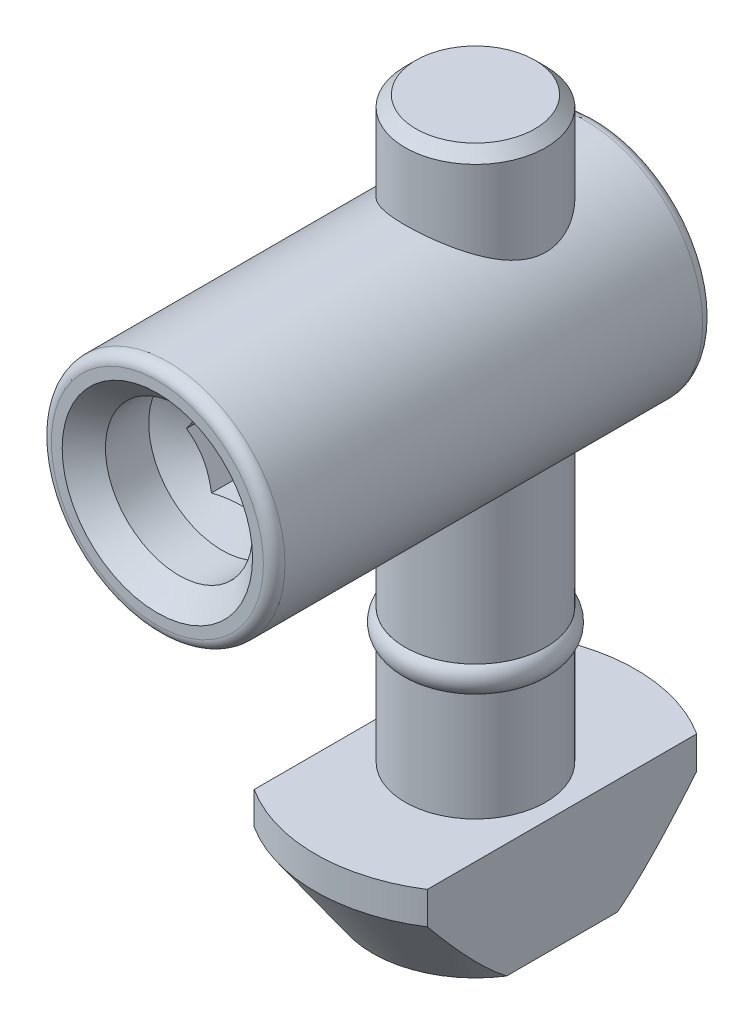
SolidWorks part; units mm, degrees
ref_plane "Спереди" through (0, 0, 0) normal (0, 0, 1) x (1, 0, 0)
ref_plane "Сверху" through (0, 0, 0) normal (0, 1, 0) x (1, 0, 0)
ref_plane "Справа" through (0, 0, 0) normal (1, 0, 0) x (0, 0, -1)
sketch "Эскиз3" plane through (0, 0, 0) normal (0, 0, 1) x (1, 0, 0)
  line L0 (0, 0) -> (-3.25, 0)
  line L1 (-3.25, 0) -> (-3.25, -20.5)
  line L2 (-3.25, -20.5) -> (-2.75, -20.5)
  line L3 (-2.75, -20.5) -> (-2.75, -21.7)
  line L4 (-2.75, -21.7) -> (-3.25, -21.7)
  line L5 (-3.25, -21.7) -> (-3.25, -26.7)
  line L7 (0, -32) -> (0, 0)
  line L8 (0, 0) -> (0, 5.384) construction
  line L9 (-3.25, -26.7) -> (-7.4, -26.7)
  line L10 (-7.4, -26.7) -> (-7.4, -28.2)
  line L11 (-7.4, -28.2) -> (-4.75, -32)
  line L12 (-4.75, -32) -> (0, -32)
  point P3 (0, -29.8286)
  point P9 (-4.2202, -32)
  dimension "D1" = 6.5
  dimension "D2" = 1.2
  dimension "D3" = 32
  dimension "D4" = 0.5
  dimension "D5" = 5
  dimension "D6" = 5.3
  dimension "D7" = 1.5
  dimension "D8" = 1.5
  dimension "D9" = 14.8
revolve "Повернуть1" add sketch "Эскиз3" angle 360 about L8
sketch "Эскиз6" plane through (0, -32, 0) normal (0, -1, 0) x (1, 0, 0)
  line L1 (-4, -7.4) -> (4, -7.4)
  line L2 (-4, -7.4) -> (-4, 7.4)
  line L3 (-4, 7.4) -> (4, 7.4)
  line L4 (4, -7.4) -> (4, 7.4)
  line L5 (-4, -7.4) -> (4, 7.4) construction
  line L6 (-4, 7.4) -> (4, -7.4) construction
  circle A1 centre (0, 0) radius 7.4 construction
  point P0 (0, 0)
  dimension "D1" = 8
extrude "Вырез-Вытянуть1" cut sketch "Эскиз6" against normal up to surface (5.3 mm away) flip side to cut up to face at (0, -26.7, -7.4)
chamfer "Фаска1" distance 0.5 angle 45 1 edges at (0, 0, -3.25)
sketch "Эскиз12" plane through (0, 0, 0) normal (0, 0, 1) x (1, 0, 0)
  line L0 (2.75, 0) -> (-2.75, 0) construction
  circle A0 centre (0, -9) radius 5.4
  point P4 (1.0261, -9)
  dimension "D1" = 10.8
  dimension "D2" = 9
extrude "Бобышка-Вытянуть2" add sketch "Эскиз12" along normal blind 14.7 and the other way blind 5.6
hole_wizard "Отверстие обработанное метчиком M81" positions "Эскиз13" profile "Эскиз14" tap size "M8" standard "ISO"
sketch "Эскиз13" plane through (0, 0, 14.7) normal (0, 0, 1) x (1, 0, 0)
  point P0 (0, -9)
cosmetic thread "Отверстие резьбы1" parameters "D1"=3, "D2"=8
sketch "Эскиз14" plane through (0, -9, 14.7) normal (1, 0, 0) x (0, -1, 0)
  line L0 (0, 0) -> (0, 5.0429)
  line L1 (0, 5.0429) -> (3.4, 3)
  line L2 (3.4, 3) -> (3.4, 1)
  line L3 (3.4, 1) -> (4.4, 0)
  line L5 (4.4, 0) -> (0, 0)
  line L6 (-3.4, 1) -> (-4.4, 0) construction
  line L10 (0, 5.0429) -> (-3.4, 3) construction
  line L11 (0, -6.35) -> (0, 107.95) construction
  dimension "Диаметр сверла" = 6.8
  dimension "Глубина сверла" = 3
  dimension "Диаметр передней зенковки" = 8.8
  dimension "Угол передней зенковки" = 90
  dimension "Угол заточки сверла" = 118
fillet "Скругление1" radius 0.5 2 edges at (5.4, -9, -5.6) (5.4, -9, 14.7)
sketch "Эскиз15" plane through (0, 0, 14.7) normal (0, 0, 1) x (1, 0, 0)
  line L1 (2.3094, -9) -> (1.1547, -7)
  line L2 (1.1547, -7) -> (-1.1547, -7)
  line L3 (-1.1547, -7) -> (-2.3094, -9)
  line L4 (-2.3094, -9) -> (-1.1547, -11)
  line L5 (-1.1547, -11) -> (1.1547, -11)
  line L6 (1.1547, -11) -> (2.3094, -9)
  circle A0 centre (0, -9) radius 2 construction
  dimension "D1" = 4
extrude "Вырез-Вытянуть2" cut sketch "Эскиз15" against normal blind 6
sketch "Эскиз16" plane through (0, 0, 0) normal (0, 0, 1) x (1, 0, 0)
  line L0 (-2.75, -20.5) -> (-3.25, -20.5)
  line L1 (-2.75, -20.5) -> (-2.75, -21.7) construction
  line L2 (-3.25, -21.7) -> (-2.75, -21.7)
  line L3 (-2.75, -21.7) -> (-2.75, -20.5)
  line L4 (-2.75, -20.5) -> (2.75, -20.5) construction
  line L7 (-3.25, -13.3125) -> (-3.25, -20.5) construction
  line L8 (3.25, -21.7) -> (-3.25, -21.7) construction
  line L9 (0, -20.5) -> (0, -21.7) construction
  arc A0 (-3.25, -20.5) -> (-3.25, -21.7) centre (-2.75, -21.1) ccw
  point P15 (-2.75, -21.1)
revolve "Повернуть2" add sketch "Эскиз16" angle 360 about L9
